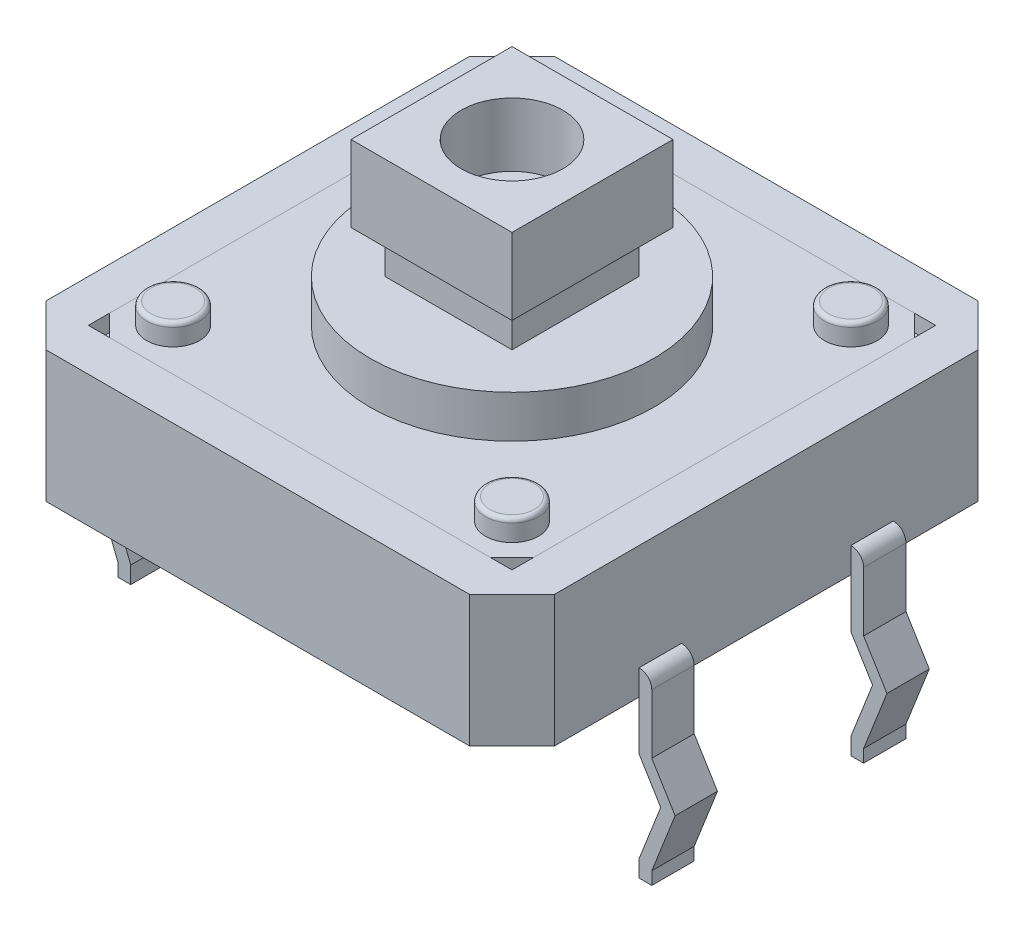
SolidWorks part; units mm, degrees
other "Markup1"
sketch "Sketch10" plane through (-6.85, 6.9, 6) normal (-0.3058, 0.046, 0.951) x (0.9335, 0.2107, 0.29)
sketch "Sketch13" plane through (-6.85, 6.9, 6) normal (-0.3058, 0.046, 0.951) x (0.9335, 0.2107, 0.29)
ref_plane "Front Plane" through (0, 0, 0) normal (0, 0, 1) x (1, 0, 0)
ref_plane "Top Plane" through (0, 0, 0) normal (0, 1, 0) x (1, 0, 0)
ref_plane "Right Plane" through (0, 0, 0) normal (1, 0, 0) x (0, 0, -1)
sketch "Sketch1" plane through (0, 0, 0) normal (0, 1, 0) x (1, 0, 0)
  line L0 (-5, 6) -> (-6, 5)
  line L1 (5, -6) -> (-5, -6)
  line L2 (6, -5) -> (6, 5)
  line L3 (5, 6) -> (-5, 6)
  line L4 (-6, -5) -> (-6, 5)
  line L5 (6, -6) -> (-6, 6) construction
  line L6 (6, 6) -> (-6, -6) construction
  line L7 (-5, -6) -> (-6, -5)
  line L8 (6, -5) -> (5, -6)
  line L9 (6, 5) -> (5, 6)
  point P0 (0, 0)
  dimension "D1" = 12
extrude "Boss-Extrude1" add sketch "Sketch1" along normal blind 3.1
sketch "Sketch2" plane through (0, 3.1, 0) normal (0, 1, 0) x (1, 0, 0)
  line L1 (5, -5) -> (-5, -5)
  line L2 (5, -5) -> (5, 5)
  line L3 (5, 5) -> (-5, 5)
  line L4 (-5, -5) -> (-5, 5)
  line L5 (5, -5) -> (-5, 5) construction
  line L6 (5, 5) -> (-5, -5) construction
  point P0 (0, 0)
  dimension "D1" = 10
extrude "Cut-Extrude1" cut sketch "Sketch2" against normal blind 0.4
sketch "Sketch3" plane through (0, 2.7, 0) normal (0, 1, 0) x (1, 0, 0)
  line L1 (4, -4) -> (-4, -4) construction
  line L2 (4, -4) -> (4, 4) construction
  line L3 (4, 4) -> (-4, 4) construction
  line L4 (-4, -4) -> (-4, 4) construction
  line L5 (4, -4) -> (-4, 4) construction
  line L6 (4, 4) -> (-4, -4) construction
  circle A0 centre (-4, 4) radius 0.625
  circle A1 centre (4, 4) radius 0.625
  circle A2 centre (-4, -4) radius 0.625
  circle A3 centre (4, -4) radius 0.625
  point P0 (0, 0)
  dimension "D2" = 1.25
  dimension "D1" = 8
extrude "Boss-Extrude2" add sketch "Sketch3" along normal blind 0.9
fillet "Fillet1" radius 0.1 4 edges at (4, 3.6, -3.375) (4, 3.6, 4.625) (-4, 3.6, 4.625) (-4, 3.6, -3.375)
sketch "Sketch4" plane through (0, 2.7, 0) normal (0, 1, 0) x (1, 0, 0)
  line L0 (5, 5) -> (-5, 5) construction
  line L1 (4.5, -5) -> (-4.5, -5)
  line L2 (5, -4.5) -> (5, 4.5)
  line L3 (4.5, 5) -> (-4.5, 5)
  line L4 (-5, -4.5) -> (-5, 4.5)
  line L5 (5, -5) -> (-5, 5) construction
  line L6 (5, 5) -> (-5, -5) construction
  line L9 (-5, 5) -> (-5, -5) construction
  line L10 (-4.5, 5) -> (-5, 4.5)
  line L11 (5, 4.5) -> (4.5, 5)
  line L12 (-4.5, -5) -> (-5, -4.5)
  line L13 (5, -4.5) -> (4.5, -5)
  circle A0 centre (0, 0) radius 3.35
  point P0 (0, 0)
  dimension "D2" = 6.7
extrude "Boss-Extrude3" add sketch "Sketch4" along normal blind 0.4 separate body
sketch "Sketch5" plane through (0, 0, 0) normal (0, 0, 1) x (1, 0, 0)
  line L1 (6, 3.1) -> (6, 0) construction
  line L2 (6, 0.6) -> (6, -1.1643)
  line L3 (6, -3.7) -> (6.3, -3.7)
  line L4 (6.3, -3.7) -> (6.3, -3.4)
  line L5 (6.3, -3.4) -> (6.85, -2)
  line L6 (6.85, -2) -> (6.3, -1.1)
  line L7 (6.3, -1.1) -> (6.3, 0.3)
  line L10 (6, -3.3) -> (6, -3.7)
  line L11 (6, 0.6) -> (6.3033, 0.6) construction
  line L12 (6.5107, -2) -> (6, -1.1643)
  line L13 (6, 0.3) -> (6.3, 0.3) construction
  line L14 (6.5107, -2) -> (6, -3.3)
  line L15 (0, -1.98) -> (0, 1.98) construction
  line L16 (-6, 0.3) -> (-6.3, 0.3) construction
  line L17 (-6, 0.6) -> (-6.3033, 0.6) construction
  line L18 (-6.5107, -2) -> (-6, -3.3)
  line L19 (-6.5107, -2) -> (-6, -1.1643)
  line L20 (-6, -3.3) -> (-6, -3.7)
  line L21 (-6.3, -1.1) -> (-6.3, 0.3)
  line L22 (-6.85, -2) -> (-6.3, -1.1)
  line L23 (-6.3, -3.4) -> (-6.85, -2)
  line L24 (-6.3, -3.7) -> (-6.3, -3.4)
  line L25 (-6, -3.7) -> (-6.3, -3.7)
  line L26 (-6, 0.6) -> (-6, -1.1643)
  arc A0 (6, 0.6) -> (6.3, 0.3) centre (6, 0.3) cw
  arc A1 (-6, 0.6) -> (-6.3, 0.3) centre (-6, 0.3) ccw
  point P15 (6.15, -3.7)
  dimension "D1" = 2.5
  dimension "D2" = 6.85
  dimension "D3" = 0.3
  dimension "D4" = 6.15
  dimension "D5" = 2
  dimension "D6" = 3.7
  dimension "D7" = 0.9
  dimension "D8" = 1.4
  dimension "D9" = 0.1
extrude "Boss-Extrude4" add sketch "Sketch5" along normal blind 3 and the other way blind 3 separate body
sketch "Sketch6" plane through (0, 0, 0) normal (0, 1, 0) x (1, 0, 0)
  line L0 (-6, 5) -> (-6, -5) construction
  line L1 (-6.85, 2) -> (-6, 2)
  line L2 (-6.85, 2) -> (-6.85, -2)
  line L3 (-6.85, -2) -> (-6, -2)
  line L4 (-6, 2) -> (-6, -2)
  line L5 (6, 2) -> (6.85, 2)
  line L6 (6, 2) -> (6, -2)
  line L7 (6, -2) -> (6.85, -2)
  line L8 (6.85, 2) -> (6.85, -2)
  line L9 (6, -5) -> (6, 5) construction
  line L10 (-6.85, 3) -> (-6.85, -3) construction
  line L11 (6.85, 3) -> (6.85, -3) construction
  point P8 (6, 0)
  point P10 (-6, 0)
  dimension "D1" = 4
extrude "Cut-Extrude2" cut sketch "Sketch6" against normal through all both and the other way through all
sketch "Sketch7" plane through (0, 2.7, 0) normal (0, 1, 0) x (1, 0, 0)
  circle A0 centre (0, 0) radius 3.35 construction
  circle A1 centre (0, 0) radius 3.35
extrude "Boss-Extrude5" add sketch "Sketch7" along normal blind 1.4 separate body
sketch "Sketch8" plane through (0, 4.1, 0) normal (0, 1, 0) x (1, 0, 0)
  line L1 (1.5, -1.5) -> (-1.5, -1.5)
  line L2 (1.5, -1.5) -> (1.5, 1.5)
  line L3 (1.5, 1.5) -> (-1.5, 1.5)
  line L4 (-1.5, -1.5) -> (-1.5, 1.5)
  line L5 (1.5, -1.5) -> (-1.5, 1.5) construction
  line L6 (1.5, 1.5) -> (-1.5, -1.5) construction
  point P0 (0, 0)
  dimension "D1" = 3
extrude "Boss-Extrude6" add sketch "Sketch8" along normal blind 1
sketch "Sketch9" plane through (0, 5.1, 0) normal (0, 1, 0) x (1, 0, 0)
  line L1 (1.9, -1.9) -> (-1.9, -1.9)
  line L2 (1.9, -1.9) -> (1.9, 1.9)
  line L3 (1.9, 1.9) -> (-1.9, 1.9)
  line L4 (-1.9, -1.9) -> (-1.9, 1.9)
  line L5 (1.9, -1.9) -> (-1.9, 1.9) construction
  line L6 (1.9, 1.9) -> (-1.9, -1.9) construction
  point P0 (0, 0)
  dimension "D1" = 3.8
extrude "Boss-Extrude7" add sketch "Sketch9" along normal blind 1.8
sketch "Sketch11" plane through (0, 6.9, 0) normal (0, 1, 0) x (1, 0, 0)
  circle A0 centre (0, 0) radius 1.2
  dimension "D1" = 2.4
extrude "Cut-Extrude3" cut sketch "Sketch11" against normal blind 1.5
sketch "Sketch12" plane through (0, 0, 0) normal (0, -1, 0) x (1, 0, 0)
  line L6 (3, 5.5) -> (3, 3.7)
  line L7 (3, 3.7) -> (5.5, 3.7)
  line L8 (5.83, 0) -> (-5.83, 0) construction
  line L9 (5.5, 4.7929) -> (5.5, -5)
  line L10 (-5, 5.5) -> (4.7929, 5.5)
  line L11 (4.7929, 5.5) -> (5.5, 4.7929)
  line L12 (5.5, 4.7929) -> (5.5, 3.7)
  line L13 (3, 5.5) -> (4.7929, 5.5)
  line L14 (4.7929, 5.5) -> (5.5, 4.7929)
  line L15 (4.7929, -5.5) -> (5.5, -4.7929)
  line L16 (3, -5.5) -> (4.7929, -5.5)
  line L17 (5.5, -4.7929) -> (5.5, -3.7)
  line L18 (3, -3.7) -> (5.5, -3.7)
  line L19 (3, -5.5) -> (3, -3.7)
  line L20 (0, -5.83) -> (0, 5.83) construction
  line L21 (-3, -5.5) -> (-3, -3.7)
  line L22 (-3, -3.7) -> (-5.5, -3.7)
  line L23 (-5.5, -4.7929) -> (-5.5, -3.7)
  line L24 (-3, -5.5) -> (-4.7929, -5.5)
  line L25 (-4.7929, -5.5) -> (-5.5, -4.7929)
  line L26 (-4.7929, 5.5) -> (-5.5, 4.7929)
  line L27 (-3, 5.5) -> (-4.7929, 5.5)
  line L28 (-5.5, 4.7929) -> (-5.5, 3.7)
  line L29 (-3, 3.7) -> (-5.5, 3.7)
  line L30 (-3, 5.5) -> (-3, 3.7)
  dimension "D2" = 2.5
  dimension "D3" = 1.8
  dimension "D1" = 0.5
extrude "Boss-Extrude8" add sketch "Sketch12" along normal blind 0.2
